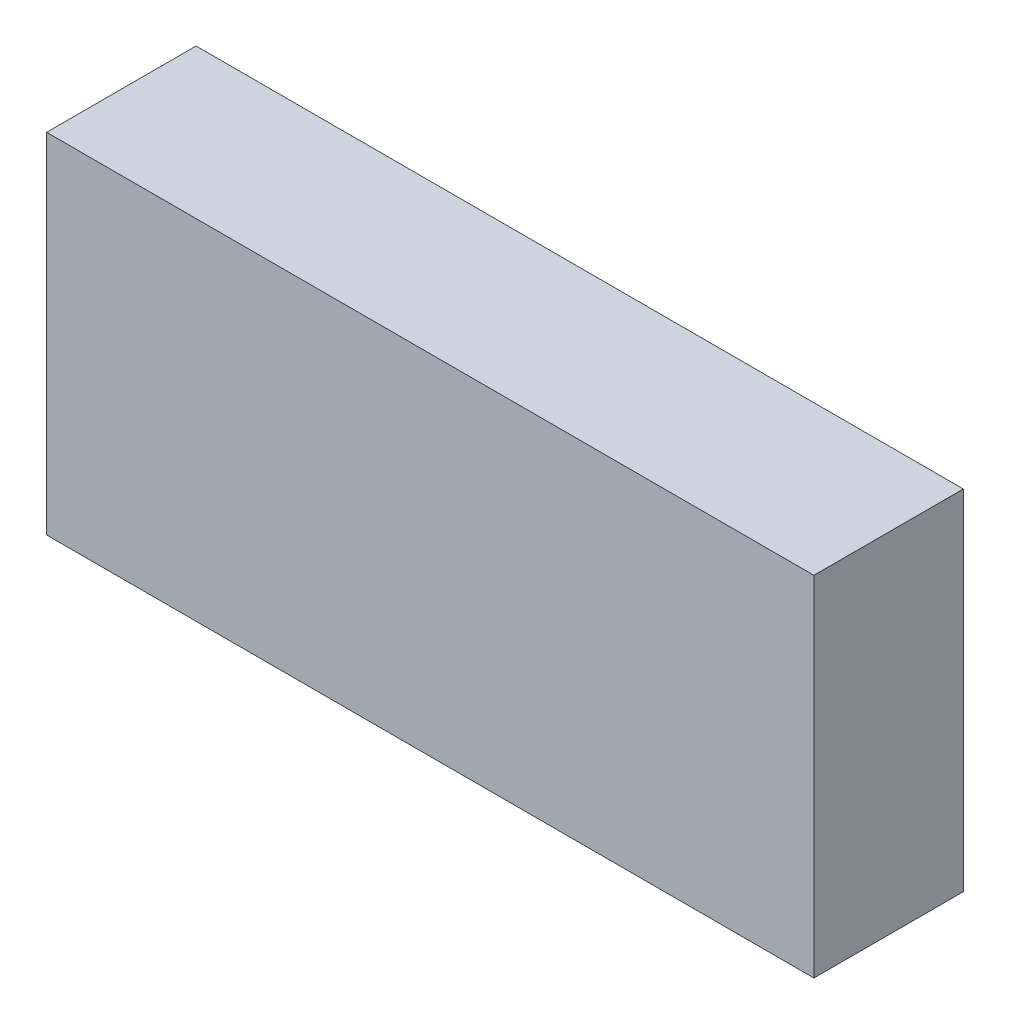
SolidWorks part; units mm, degrees
ref_plane "Front Plane" through (0, 0, 0) normal (0, 0, 1) x (1, 0, 0)
ref_plane "Top Plane" through (0, 0, 0) normal (0, 1, 0) x (1, 0, 0)
ref_plane "Right Plane" through (0, 0, 0) normal (1, 0, 0) x (0, 0, -1)
sketch "Эскиз1" plane through (0, 0, 0) normal (0, 0, 1) x (1, 0, 0)
  line L1 (-38.5, -17.5) -> (38.5, -17.5)
  line L2 (-38.5, -17.5) -> (-38.5, 17.5)
  line L3 (-38.5, 17.5) -> (38.5, 17.5)
  line L4 (38.5, -17.5) -> (38.5, 17.5)
  line L5 (-38.5, -17.5) -> (38.5, 17.5) construction
  line L6 (-38.5, 17.5) -> (38.5, -17.5) construction
  point P0 (0, 0)
  dimension "D1" = 35
  dimension "D2" = 77
extrude "Бобышка-Вытянуть1" add sketch "Эскиз1" along normal mid plane 15
